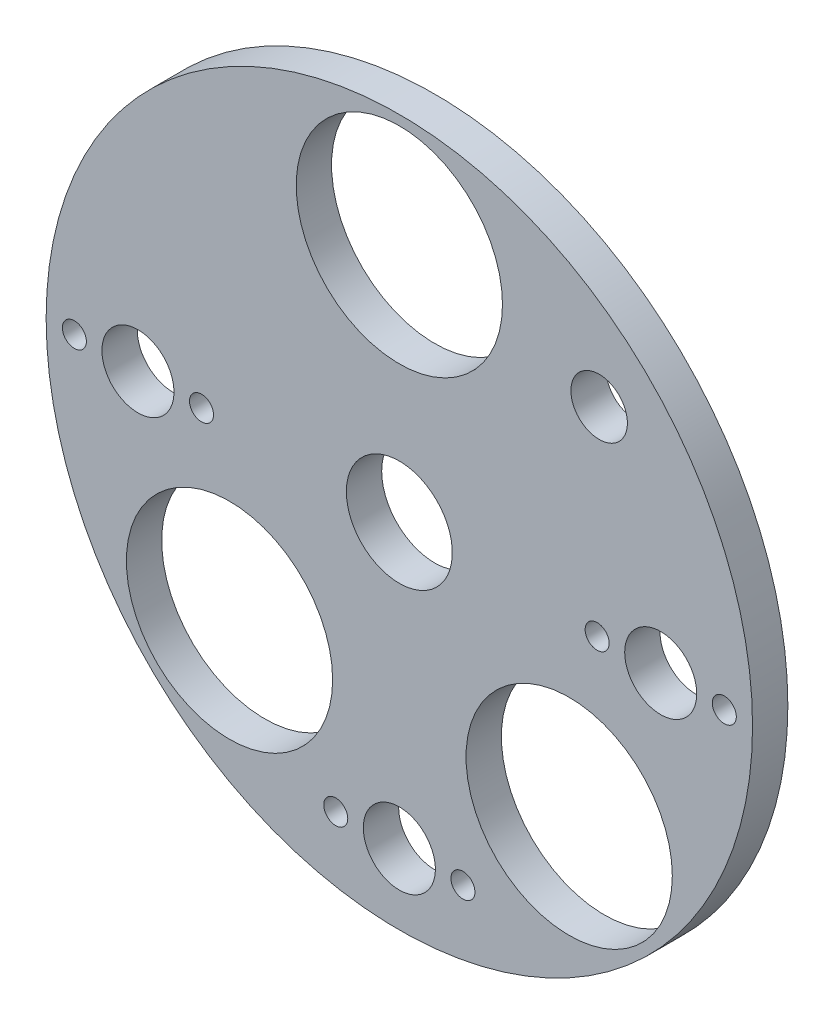
SolidWorks part; units mm, degrees
material "Acrylic (Medium-high impact)"
ref_plane "Front Plane" through (0, 0, 0) normal (0, 0, 1) x (1, 0, 0)
ref_plane "Top Plane" through (0, 0, 0) normal (0, 1, 0) x (1, 0, 0)
ref_plane "Right Plane" through (0, 0, 0) normal (1, 0, 0) x (0, 0, -1)
sketch "Sketch1" plane through (0, 0, 0) normal (0, 0, 1) x (1, 0, 0)
  circle A0 centre (0, 0) radius 50
  dimension "D1" = 100
extrude "Boss-Extrude1" add sketch "Sketch1" along normal blind 5
hole_wizard "Ø15.0 (15) Diameter Hole1" positions "Sketch3" profile "Sketch4" hole size "Ø15.0" standard "ISO" end condition through all
sketch "Sketch3" plane through (0, 0, 0) normal (0, 0, -1) x (-1, 0, 0)
  point P0 (0, 0)
sketch "Sketch4" plane through (0, 0, 0) normal (1, 0, 0) x (0, 1, 0)
  line L0 (0, 0) -> (0, 5)
  line L1 (0, 5) -> (7.5, 5)
  line L2 (7.5, 5) -> (7.5, 0)
  line L5 (7.5, 0) -> (0, 0)
  line L11 (0, -6.35) -> (0, 107.95) construction
  dimension "Thru Hole Dia." = 15
  dimension "Thru Hole Depth" = 5
hole_wizard "Ø10.2 (10.2) Diameter Hole1" positions "Sketch5" profile "Sketch6" hole size "Ø10.2" standard "ISO"
sketch "Sketch5" plane through (0, 0, 0) normal (0, 0, -1) x (-1, 0, 0)
  point P4 (37, 0)
  point P17 (-37, 0)
  point P18 (0, 0)
  point P21 (0, -37)
  point P23 (0, -40)
  dimension "D1" = 3
  dimension "D2" = 40
  dimension "D3" = 37
sketch "Sketch6" plane through (-37, 0, 0) normal (1, 0, 0) x (0, 1, 0)
  line L0 (0, 0) -> (0, 5)
  line L1 (0, 5) -> (5.1, 5)
  line L2 (5.1, 5) -> (5.1, 0)
  line L5 (5.1, 0) -> (0, 0)
  line L11 (0, -6.35) -> (0, 107.95) construction
  dimension "Thru Hole Dia." = 10.2
  dimension "Thru Hole Depth" = 5
hole_wizard "M3 Clearance Hole1" positions "Sketch7" profile "Sketch8" hole size "M3" standard "ISO" end condition through all
sketch "Sketch7" plane through (0, 0, 5) normal (0, 0, 1) x (1, 0, 0)
  circle A0 centre (37, 0) radius 5.1 construction
  circle A1 centre (0, -40) radius 5.1 construction
  point P0 (46, 0)
  point P2 (28, 0)
  point P11 (9, -40)
  point P13 (-9, -40)
  point P46 (-46, 0)
  point P47 (-28, 0)
  dimension "D2" = 9
  dimension "D1" = 9
  dimension "D4" = 9
  dimension "D5" = 9
  dimension "D6" = 2
  dimension "D3" = 40
sketch "Sketch8" plane through (46, 0, 5) normal (1, 0, 0) x (0, -1, 0)
  line L0 (0, 0) -> (0, 5)
  line L1 (0, 5) -> (1.7, 5)
  line L2 (1.7, 5) -> (1.7, 0)
  line L5 (1.7, 0) -> (0, 0)
  line L11 (0, -6.35) -> (0, 107.95) construction
  dimension "Thru Hole Dia." = 3.4
  dimension "Thru Hole Depth" = 5
sketch "Sketch9" plane through (0, 0, 5) normal (0, 0, 1) x (1, 0, 0)
  line L0 (0, 0) -> (24.0416, -24.0416) construction
  line L1 (0, 0) -> (71.3708, 0) construction
  circle A0 centre (24.0416, -24.0416) radius 14.6
  circle A2 centre (-24.0416, -24.0416) radius 14.6
  circle A4 centre (0, 34) radius 14.6
  point P13 (0, 0)
  dimension "D1" = 29.2
  dimension "D3" = 45
  dimension "D7" = 29.2
  dimension "D2" = 34
  dimension "D8" = 34
  dimension "D6" = 2
extrude "Cut-Extrude1" cut sketch "Sketch9" against normal blind 10
sketch "Sketch10" plane through (0, 0, 5) normal (0, 0, 1) x (1, 0, 0)
  line L0 (0, 0) -> (28.2843, 28.2843) construction
  line L1 (0, 0) -> (-59.3945, 0) construction
  circle A0 centre (28.2843, 28.2843) radius 4
  dimension "D1" = 8
  dimension "D2" = 40
  dimension "D3" = 135
extrude "Cut-Extrude2" cut sketch "Sketch10" against normal blind 10
